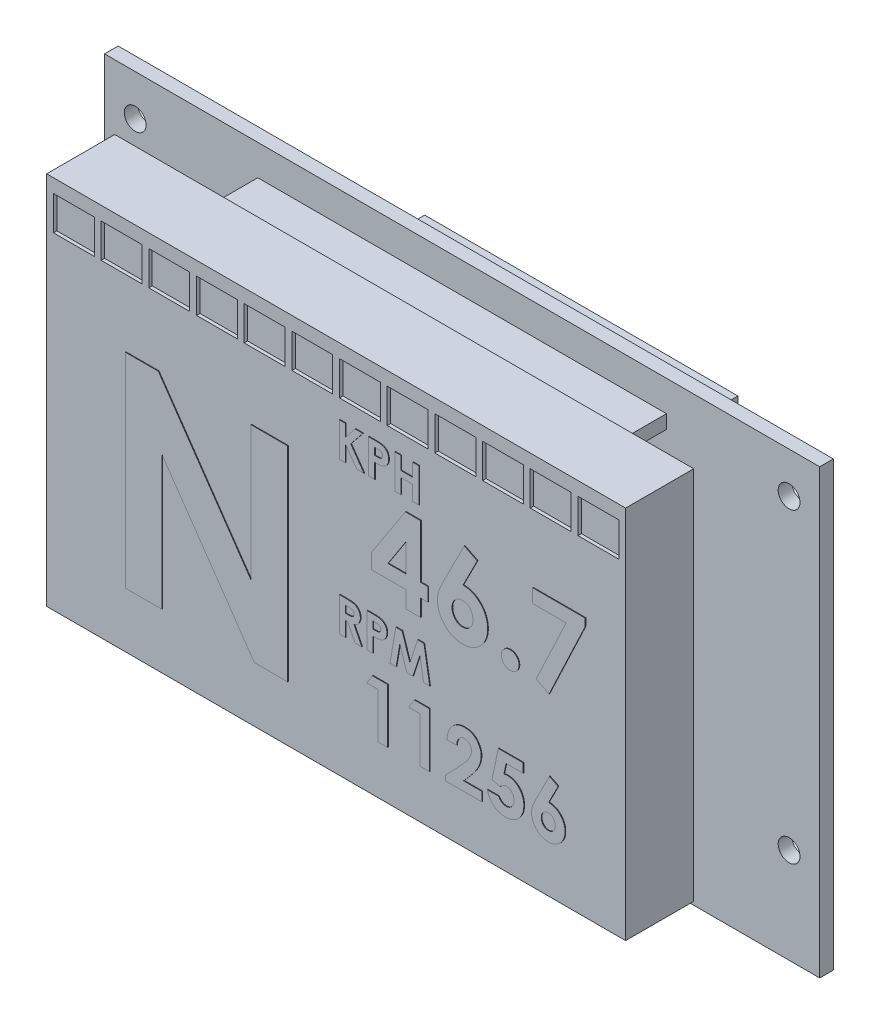
SolidWorks part; units mm, degrees
ref_plane "正面" through (0, 0, 0) normal (0, 0, 1) x (1, 0, 0)
ref_plane "平面" through (0, 0, 0) normal (0, 1, 0) x (1, 0, 0)
ref_plane "右側面" through (0, 0, 0) normal (1, 0, 0) x (0, 0, -1)
sketch "ｽｹｯﾁ1" plane through (0, 0, 0) normal (0, 0, 1) x (1, 0, 0)
  line L1 (52.5, 33.5) -> (-52.5, 33.5)
  line L2 (52.5, 33.5) -> (52.5, -33.5)
  line L3 (52.5, -33.5) -> (-52.5, -33.5)
  line L4 (-52.5, 33.5) -> (-52.5, -33.5)
  line L5 (52.5, 33.5) -> (-52.5, -33.5) construction
  line L6 (52.5, -33.5) -> (-52.5, 33.5) construction
  point P0 (0, 0)
  dimension "D1" = 67
  dimension "D2" = 105
extrude "ﾎﾞｽ - 押し出し1" add sketch "ｽｹｯﾁ1" along normal blind 2
sketch "ｽｹｯﾁ2" plane through (0, 0, 2) normal (0, 0, 1) x (1, 0, 0)
  line L0 (52.5, 33.5) -> (-52.5, 33.5) construction
  line L5 (-52.5, -33.5) -> (52.5, -33.5) construction
  line L10 (0, 0) -> (0, -33.5) construction
  circle A0 centre (48, 17.5) radius 1.6
  circle A3 centre (48, -27.5) radius 1.6
  circle A4 centre (-48, -27.5) radius 1.6
  circle A5 centre (-48, 17.5) radius 1.6
  dimension "D1" = 3.2
  dimension "D3" = 48
  dimension "D4" = 3.2
  dimension "D5" = 45
  dimension "D2" = 16
extrude "ｶｯﾄ - 押し出し1" cut sketch "ｽｹｯﾁ2" against normal through all
sketch "ｽｹｯﾁ3" plane through (0, 0, 2) normal (0, 0, 1) x (1, 0, 0)
  line L0 (52.5, 33.5) -> (-52.5, 33.5) construction
  line L1 (-45, 29.5) -> (45, 29.5)
  line L2 (-45, 29.5) -> (-45, 27.5)
  line L3 (-45, 27.5) -> (45, 27.5)
  line L4 (45, 29.5) -> (45, 27.5)
  line L5 (-45, 29.5) -> (45, 27.5) construction
  line L6 (-45, 27.5) -> (45, 29.5) construction
  point P0 (0, 28.5)
  dimension "D1" = 2
  dimension "D2" = 5
  dimension "D3" = 90
sketch "ｽｹｯﾁ5" plane through (0, 0, 2) normal (0, 0, 1) x (1, 0, 0)
  line L0 (-52.5, -33.5) -> (52.5, -33.5) construction
  line L1 (-30, 19) -> (30, 19)
  line L2 (-30, 19) -> (-30, 17)
  line L3 (-30, 17) -> (30, 17)
  line L4 (30, 19) -> (30, 17)
  line L5 (-30, 19) -> (30, 17) construction
  line L6 (-30, 17) -> (30, 19) construction
  line L7 (-30, -29) -> (30, -29)
  line L8 (-30, -29) -> (-30, -31)
  line L9 (-30, -31) -> (30, -31)
  line L10 (30, -29) -> (30, -31)
  line L11 (-30, -29) -> (30, -31) construction
  line L12 (-30, -31) -> (30, -29) construction
  point P0 (0, 18)
  point P5 (0, -30)
  dimension "D1" = 2
  dimension "D2" = 60
  dimension "D3" = 2
  dimension "D4" = 60
  dimension "D5" = 2.5
  dimension "D6" = 48
extrude "ﾎﾞｽ - 押し出し4" add sketch "ｽｹｯﾁ5" along normal blind 8.5
sketch "ｽｹｯﾁ6" plane through (0, 0, 10.5) normal (0, 0, 1) x (1, 0, 0)
  line L0 (-52.5, -33.5) -> (52.5, -33.5) construction
  line L1 (42.5, 22.5) -> (-42.5, 22.5)
  line L2 (42.5, 22.5) -> (42.5, -32.5)
  line L3 (42.5, -32.5) -> (-42.5, -32.5)
  line L4 (-42.5, 22.5) -> (-42.5, -32.5)
  line L5 (42.5, 22.5) -> (-42.5, -32.5) construction
  line L6 (42.5, -32.5) -> (-42.5, 22.5) construction
  point P0 (0, -5)
  dimension "D1" = 85
  dimension "D2" = 55
  dimension "D3" = 1
extrude "ﾎﾞｽ - 押し出し5" add sketch "ｽｹｯﾁ6" along normal blind 10
sketch "ｽｹｯﾁ7" plane through (0, 0, 0) normal (0, 0, -1) x (-1, 0, 0)
  line L0 (0, 0) -> (0, -33.5) construction
  line L1 (-26, 20) -> (-28, 20)
  line L2 (-26, 20) -> (-26, -20)
  line L3 (-26, -20) -> (-28, -20)
  line L4 (-28, 20) -> (-28, -20)
  line L5 (-26, 20) -> (-28, -20) construction
  line L6 (-26, -20) -> (-28, 20) construction
  line L7 (-12, 20) -> (-10, 20)
  line L8 (-12, 20) -> (-12, -20)
  line L9 (-12, -20) -> (-10, -20)
  line L10 (-10, 20) -> (-10, -20)
  line L11 (-12, 20) -> (-10, -20) construction
  line L12 (-12, -20) -> (-10, 20) construction
  line L13 (52.5, -33.5) -> (-52.5, -33.5) construction
  line L14 (12, -20) -> (10, -20)
  line L15 (10, 20) -> (10, -20)
  line L16 (12, 20) -> (12, -20)
  line L17 (12, 20) -> (10, 20)
  line L18 (26, 20) -> (28, 20)
  line L19 (26, 20) -> (26, -20)
  line L20 (26, -20) -> (28, -20)
  line L21 (28, 20) -> (28, -20)
  point P0 (-27, 0)
  point P5 (-11, 0)
  dimension "D1" = 2
  dimension "D2" = 40
  dimension "D3" = 40
  dimension "D4" = 2
  dimension "D5" = 10
  dimension "D6" = 14
sketch "ｽｹｯﾁ10" plane through (0, 0, 20.5) normal (0, 0, 1) x (1, 0, 0)
  text T0 "N" font "Century Gothic" height 30
extrude "ﾎﾞｽ - 押し出し8" add sketch "ｽｹｯﾁ10" along normal blind 0.1
sketch "ｽｹｯﾁ11" plane through (0, 0, 20.5) normal (0, 0, 1) x (1, 0, 0)
  text T0 "Gear\r\n" font "Century Gothic" height 7
sketch "ｽｹｯﾁ12" plane through (0, 0, 20.5) normal (0, 0, 1) x (1, 0, 0)
  text T0 "KPH" font "Century Gothic" height 5
extrude "ﾎﾞｽ - 押し出し10" add sketch "ｽｹｯﾁ12" along normal blind 0.1
sketch "ｽｹｯﾁ13" plane through (0, 0, 20.5) normal (0, 0, 1) x (1, 0, 0)
  text T0 "46.7" font "Century Gothic" height 12
extrude "ﾎﾞｽ - 押し出し11" add sketch "ｽｹｯﾁ13" along normal blind 0.1
sketch "ｽｹｯﾁ14" plane through (0, 0, 20.5) normal (0, 0, 1) x (1, 0, 0)
  text T0 "RPM" font "Century Gothic" height 5
extrude "ﾎﾞｽ - 押し出し12" add sketch "ｽｹｯﾁ14" along normal blind 0.1
sketch "ｽｹｯﾁ15" plane through (0, 0, 20.5) normal (0, 0, 1) x (1, 0, 0)
  text T0 "11256" font "Century Gothic" height 8
extrude "ﾎﾞｽ - 押し出し13" add sketch "ｽｹｯﾁ15" along normal blind 0.1
sketch "ｽｹｯﾁ16" plane through (0, 0, 0) normal (0, 0, -1) x (-1, 0, 0)
  line L1 (-45.5, 21.5) -> (-2.5, 21.5)
  line L2 (-45.5, 21.5) -> (-45.5, 19.5)
  line L3 (-45.5, 19.5) -> (-2.5, 19.5)
  line L4 (-2.5, 21.5) -> (-2.5, 19.5)
  line L5 (-45.5, 21.5) -> (-2.5, 19.5) construction
  line L6 (-45.5, 19.5) -> (-2.5, 21.5) construction
  line L7 (-45.5, 5.5) -> (-2.5, 5.5)
  line L8 (-45.5, 5.5) -> (-45.5, 3.5)
  line L9 (-45.5, 3.5) -> (-2.5, 3.5)
  line L10 (-2.5, 5.5) -> (-2.5, 3.5)
  line L11 (-45.5, 5.5) -> (-2.5, 3.5) construction
  line L12 (-45.5, 3.5) -> (-2.5, 5.5) construction
  line L13 (0, 0) -> (0, -33.5) construction
  line L14 (52.5, -33.5) -> (-52.5, -33.5) construction
  line L15 (45.5, 19.5) -> (2.5, 19.5)
  line L16 (2.5, 21.5) -> (2.5, 19.5)
  line L17 (45.5, 21.5) -> (2.5, 21.5)
  line L18 (45.5, 21.5) -> (45.5, 19.5)
  line L19 (45.5, 3.5) -> (2.5, 3.5)
  line L20 (2.5, 5.5) -> (2.5, 3.5)
  line L21 (45.5, 5.5) -> (2.5, 5.5)
  line L22 (45.5, 5.5) -> (45.5, 3.5)
  line L24 (-52.5, 33.5) -> (52.5, 33.5) construction
  point P0 (-24, 20.5)
  point P5 (-24, 4.5)
  dimension "D1" = 2
  dimension "D2" = 43
  dimension "D3" = 2
  dimension "D4" = 43
  dimension "D5" = 14
  dimension "D6" = 2.5
  dimension "D7" = 12
sketch "ｽｹｯﾁ17" plane through (0, 0, 0) normal (0, 0, -1) x (-1, 0, 0)
  circle A0 centre (-48, 17.5) radius 3 construction
  dimension "D1" = 6
sketch "ｽｹｯﾁ18" plane through (0, 0, 2) normal (0, 0, 1) x (1, 0, 0)
  line L0 (-52.5, 33.5) -> (-52.5, 23.5)
  line L1 (-52.5, 33.5) -> (-52.5, -33.5) construction
  line L2 (-52.5, 23.5) -> (52.5, 23.5)
  line L3 (52.5, -33.5) -> (52.5, 33.5) construction
  line L4 (52.5, 23.5) -> (52.5, 33.5)
  line L5 (52.5, 33.5) -> (-52.5, 33.5)
  dimension "D1" = 10
extrude "ｶｯﾄ - 押し出し2" cut sketch "ｽｹｯﾁ18" against normal blind 10
sketch "ｽｹｯﾁ19" plane through (0, 0, 0) normal (0, 0, -1) x (-1, 0, 0)
  line L0 (-52.5, 23.5) -> (52.5, 23.5) construction
  line L1 (-22.5, 8.5) -> (22.5, 8.5)
  line L2 (-22.5, 8.5) -> (-22.5, 6)
  line L3 (-22.5, 6) -> (22.5, 6)
  line L4 (22.5, 8.5) -> (22.5, 6)
  line L5 (-22.5, 8.5) -> (22.5, 6) construction
  line L6 (-22.5, 6) -> (22.5, 8.5) construction
  line L7 (-22.5, -7) -> (22.5, -7)
  line L8 (-22.5, -7) -> (-22.5, -9.5)
  line L9 (-22.5, -9.5) -> (22.5, -9.5)
  line L10 (22.5, -7) -> (22.5, -9.5)
  line L11 (-22.5, -7) -> (22.5, -9.5) construction
  line L12 (-22.5, -9.5) -> (22.5, -7) construction
  line L14 (-52.5, -33.5) -> (-52.5, 23.5) construction
  circle A0 centre (-48.5, 16.5) radius 3 construction
  point P0 (0, 7.25)
  point P5 (0, -8.25)
  dimension "D7" = 6
  dimension "D1" = 2.5
  dimension "D2" = 2.5
  dimension "D3" = 45
  dimension "D4" = 15
  dimension "45" = 45
  dimension "D5" = 18
  dimension "D6" = 7
  dimension "D8" = 4
extrude "ﾎﾞｽ - 押し出し14" add sketch "ｽｹｯﾁ19" along normal blind 8.5
sketch "ｽｹｯﾁ20" plane through (0, 0, 0) normal (0, 0, -1) x (-1, 0, 0)
  line L0 (52.5, 23.5) -> (52.5, -33.5) construction
  line L1 (0, 13.3116) -> (48, 13.3116)
  line L2 (0, 13.3116) -> (0, -7.6884)
  line L3 (0, -7.6884) -> (48, -7.6884)
  line L4 (48, 13.3116) -> (48, -7.6884)
  line L5 (0, 13.3116) -> (48, -7.6884) construction
  line L6 (0, -7.6884) -> (48, 13.3116) construction
  line L7 (1.5, 11.8116) -> (46.5, 11.8116) construction
  line L8 (1.5, 11.8116) -> (1.5, -6.1884) construction
  line L9 (1.5, -6.1884) -> (46.5, -6.1884) construction
  line L10 (46.5, 11.8116) -> (46.5, -6.1884) construction
  line L11 (1.5, 11.8116) -> (46.5, -6.1884) construction
  line L12 (1.5, -6.1884) -> (46.5, 11.8116) construction
  point P0 (24, 2.8116)
  point P5 (24, 2.8116)
  dimension "D1" = 21
  dimension "D2" = 48
  dimension "D3" = 18
  dimension "D4" = 45
  dimension "D5" = 6
sketch "ｽｹｯﾁ21" plane through (0, 0, 0) normal (0, 0, -1) x (-1, 0, 0)
  line L1 (-24, -6) -> (24, -6)
  line L2 (-24, -6) -> (-24, -27)
  line L3 (-24, -27) -> (24, -27)
  line L4 (24, -6) -> (24, -27)
  line L5 (-24, -6) -> (24, -27) construction
  line L6 (-24, -27) -> (24, -6) construction
  line L8 (-30, -29) -> (30, -29) construction
  point P0 (0, -16.5)
  dimension "D1" = 21
  dimension "D2" = 48
  dimension "D3" = 2
sketch "ｽｹｯﾁ22" plane through (0, 0, -8.5) normal (0, 0, -1) x (-1, 0, 0)
  line L0 (22.5, 8.5) -> (-22.5, 8.5) construction
  line L1 (-23, 9) -> (23, 9)
  line L2 (-23, 9) -> (-23, -10)
  line L3 (-23, -10) -> (23, -10)
  line L4 (23, 9) -> (23, -10)
  line L5 (-23, 9) -> (23, -10) construction
  line L6 (-23, -10) -> (23, 9) construction
  line L7 (-22.5, -7) -> (-22.5, -9.5) construction
  point P0 (0, -0.5)
  dimension "D1" = 46
  dimension "D2" = 19
  dimension "D3" = 0.5
  dimension "D4" = 0.5
extrude "ﾎﾞｽ - 押し出し15" add sketch "ｽｹｯﾁ22" along normal blind 7
sketch "ｽｹｯﾁ23" plane through (0, 0, -8.5) normal (0, 0, 1) x (1, 0, 0)
  line L0 (-23, 9) -> (23, 9) construction
  line L1 (23, 3) -> (14.9844, 3)
  line L2 (23, 3) -> (23, -4)
  line L3 (23, -4) -> (14.9844, -4)
  line L4 (14.9844, 3) -> (14.9844, -4)
  line L5 (23, 3) -> (14.9844, -4) construction
  line L6 (23, -4) -> (14.9844, 3) construction
  line L7 (23, 9) -> (23, -10) construction
  point P0 (18.9922, -0.5)
  dimension "D1" = 7
  dimension "D2" = 6
sketch "ｽｹｯﾁ25" plane through (0, 0, 0) normal (0, 0, -1) x (-1, 0, 0)
  line L0 (22.5, 8.5) -> (-22.5, 8.5) construction
  line L1 (-25, 31.5) -> (25, 31.5)
  line L2 (-25, 31.5) -> (-25, 10.5)
  line L3 (-25, 10.5) -> (25, 10.5)
  line L4 (25, 31.5) -> (25, 10.5)
  line L5 (-25, 31.5) -> (25, 10.5) construction
  line L6 (-25, 10.5) -> (25, 31.5) construction
  point P0 (0, 21)
  dimension "D1" = 21
  dimension "D2" = 50
  dimension "D3" = 2
sketch "ｽｹｯﾁ26" plane through (0, 0, 0) normal (0, 0, -1) x (-1, 0, 0)
  line L1 (-25, -11.5) -> (25, -11.5)
  line L2 (-25, -11.5) -> (-25, -32.5)
  line L3 (-25, -32.5) -> (25, -32.5)
  line L4 (25, -11.5) -> (25, -32.5)
  line L5 (-25, -11.5) -> (25, -32.5) construction
  line L6 (-25, -32.5) -> (25, -11.5) construction
  line L7 (-22.5, -9.5) -> (22.5, -9.5) construction
  point P0 (0, -22)
  dimension "D1" = 21
  dimension "D2" = 50
  dimension "D3" = 2
sketch "ｽｹｯﾁ28" plane through (0, 0, 2) normal (0, 0, 1) x (1, 0, 0)
  line L0 (-52.5, -33.5) -> (-52.5, -41.5)
  line L1 (-52.5, -41.5) -> (52.5, -41.5)
  line L2 (52.5, -41.5) -> (52.5, -33.5)
  line L3 (52.5, -33.5) -> (-52.5, -33.5)
  dimension "D1" = 8
extrude "ﾎﾞｽ - 押し出し16" add sketch "ｽｹｯﾁ28" against normal blind 2
sketch "ｽｹｯﾁ29" plane through (0, 0, 20.5) normal (0, 0, 1) x (1, 0, 0)
  line L0 (42.5, -32.5) -> (42.5, 22.5) construction
  line L1 (41.5, 20.5) -> (35.5, 20.5)
  line L2 (41.5, 20.5) -> (41.5, 15.5)
  line L3 (41.5, 15.5) -> (35.5, 15.5)
  line L4 (35.5, 20.5) -> (35.5, 15.5)
  line L5 (41.5, 20.5) -> (35.5, 15.5) construction
  line L6 (41.5, 15.5) -> (35.5, 20.5) construction
  line L7 (42.5, 22.5) -> (-42.5, 22.5) construction
  line L8 (28.5, 20.5) -> (28.5, 15.5)
  line L9 (34.5, 15.5) -> (28.5, 15.5)
  line L10 (34.5, 20.5) -> (28.5, 20.5)
  line L11 (34.5, 20.5) -> (34.5, 15.5)
  line L12 (21.5, 20.5) -> (21.5, 15.5)
  line L13 (27.5, 15.5) -> (21.5, 15.5)
  line L14 (27.5, 20.5) -> (21.5, 20.5)
  line L15 (27.5, 20.5) -> (27.5, 15.5)
  line L16 (14.5, 20.5) -> (14.5, 15.5)
  line L17 (20.5, 15.5) -> (14.5, 15.5)
  line L18 (20.5, 20.5) -> (14.5, 20.5)
  line L19 (20.5, 20.5) -> (20.5, 15.5)
  line L20 (7.5, 20.5) -> (7.5, 15.5)
  line L21 (13.5, 15.5) -> (7.5, 15.5)
  line L22 (13.5, 20.5) -> (7.5, 20.5)
  line L23 (13.5, 20.5) -> (13.5, 15.5)
  line L24 (0.5, 20.5) -> (0.5, 15.5)
  line L25 (6.5, 15.5) -> (0.5, 15.5)
  line L26 (6.5, 20.5) -> (0.5, 20.5)
  line L27 (6.5, 20.5) -> (6.5, 15.5)
  line L28 (-6.5, 20.5) -> (-6.5, 15.5)
  line L29 (-0.5, 15.5) -> (-6.5, 15.5)
  line L30 (-0.5, 20.5) -> (-6.5, 20.5)
  line L31 (-0.5, 20.5) -> (-0.5, 15.5)
  line L32 (-13.5, 20.5) -> (-13.5, 15.5)
  line L33 (-7.5, 15.5) -> (-13.5, 15.5)
  line L34 (-7.5, 20.5) -> (-13.5, 20.5)
  line L35 (-7.5, 20.5) -> (-7.5, 15.5)
  line L36 (-20.5, 20.5) -> (-20.5, 15.5)
  line L37 (-14.5, 15.5) -> (-20.5, 15.5)
  line L38 (-14.5, 20.5) -> (-20.5, 20.5)
  line L39 (-14.5, 20.5) -> (-14.5, 15.5)
  line L40 (-27.5, 20.5) -> (-27.5, 15.5)
  line L41 (-21.5, 15.5) -> (-27.5, 15.5)
  line L42 (-21.5, 20.5) -> (-27.5, 20.5)
  line L43 (-21.5, 20.5) -> (-21.5, 15.5)
  line L44 (-34.5, 20.5) -> (-34.5, 15.5)
  line L45 (-28.5, 15.5) -> (-34.5, 15.5)
  line L46 (-28.5, 20.5) -> (-34.5, 20.5)
  line L47 (-28.5, 20.5) -> (-28.5, 15.5)
  line L48 (-41.5, 20.5) -> (-41.5, 15.5)
  line L49 (-35.5, 15.5) -> (-41.5, 15.5)
  line L50 (-35.5, 20.5) -> (-41.5, 20.5)
  line L51 (-35.5, 20.5) -> (-35.5, 15.5)
  point P0 (38.5, 18)
  dimension "D1" = 6
  dimension "D2" = 1
  dimension "D3" = 5
  dimension "D4" = 2
  dimension "D5" = 12
extrude "ｶｯﾄ - 押し出し3" cut sketch "ｽｹｯﾁ29" against normal blind 0.5
